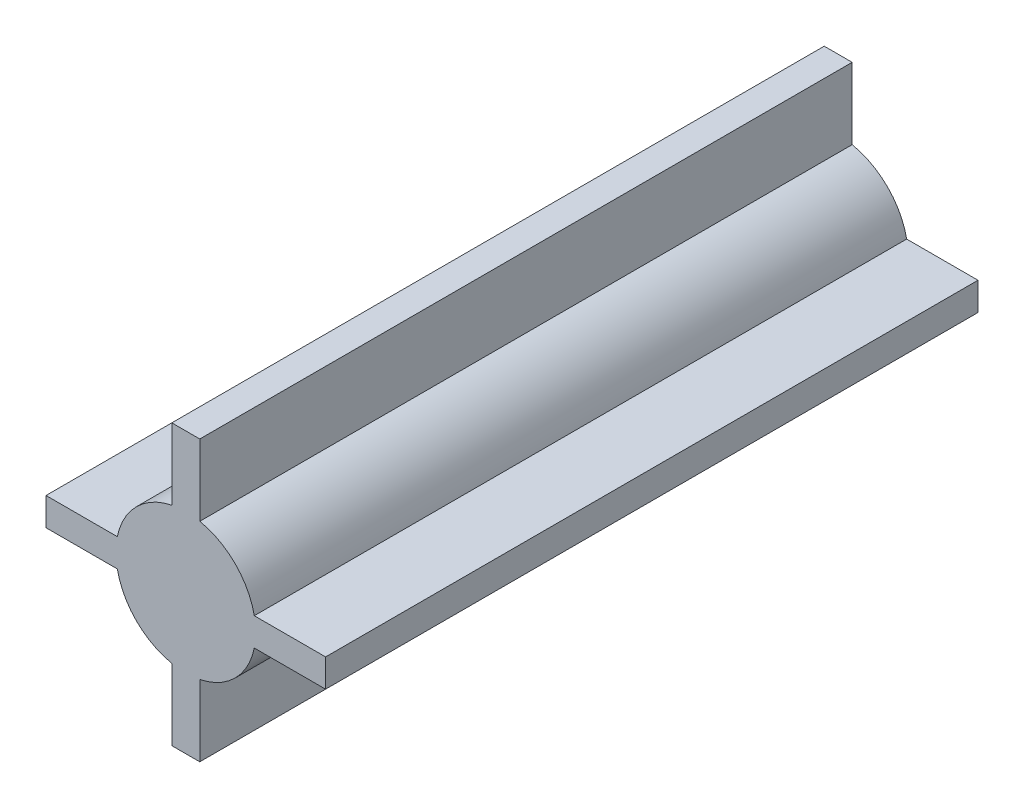
SolidWorks part; units mm, degrees
ref_plane "Front Plane" through (0, 0, 0) normal (0, 0, 1) x (1, 0, 0)
ref_plane "Top Plane" through (0, 0, 0) normal (0, 1, 0) x (1, 0, 0)
ref_plane "Right Plane" through (0, 0, 0) normal (1, 0, 0) x (0, 0, -1)
sketch "Sketch1" plane through (0, 0, 0) normal (0, 0, 1) x (1, 0, 0)
  line L0 (1.5, -15) -> (1.5, 15)
  line L1 (15, -1.5) -> (-15, -1.5)
  line L2 (15, -1.5) -> (15, 1.5)
  line L3 (15, 1.5) -> (-15, 1.5)
  line L4 (-15, -1.5) -> (-15, 1.5)
  line L5 (15, -1.5) -> (-15, 1.5) construction
  line L6 (15, 1.5) -> (-15, -1.5) construction
  line L7 (-1.5, -15) -> (1.5, -15)
  line L8 (-1.5, -15) -> (-1.5, 15)
  line L9 (-1.5, 15) -> (1.5, 15)
  line L10 (-15, -1.5) -> (15, -1.5)
  line L11 (-15, 1.5) -> (-15, -1.5)
  line L12 (-15, 1.5) -> (15, 1.5)
  line L13 (15, 1.5) -> (15, -1.5)
  line L14 (-1.5, 15) -> (-1.5, -15)
  line L15 (1.5, 15) -> (-1.5, 15)
  line L16 (1.5, 15) -> (1.5, -15)
  line L17 (1.5, -15) -> (-1.5, -15)
  circle A0 centre (0, 0) radius 7.5
  point P22 (0, 0)
  dimension "D1" = 15
  dimension "D2" = 30
  dimension "D3" = 3
  dimension "D5" = 15
  dimension "D6" = 15.0748
  dimension "D4" = 4
extrude "Boss-Extrude2" add sketch "Sketch1" along normal blind 70 contours L2 L1 L4 L3 | L14 L17 L16 L15 | A0
